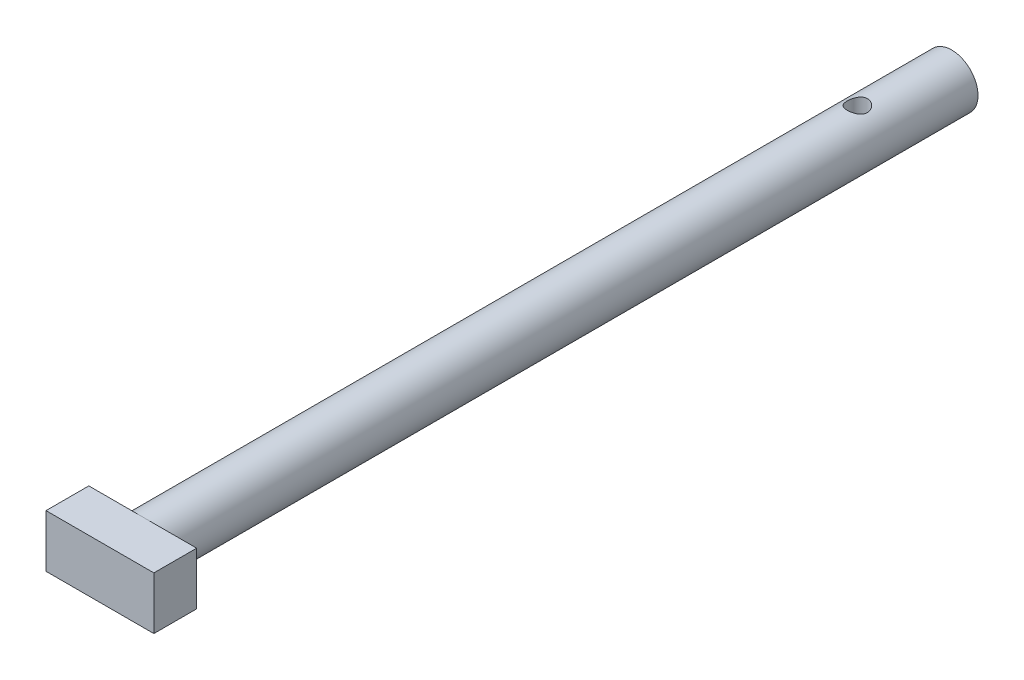
SolidWorks part; units mm, degrees
ref_plane "Front Plane" through (0, 0, 0) normal (0, 0, 1) x (1, 0, 0)
ref_plane "Top Plane" through (0, 0, 0) normal (0, 1, 0) x (1, 0, 0)
ref_plane "Right Plane" through (0, 0, 0) normal (1, 0, 0) x (0, 0, -1)
sketch "Sketch1" plane through (0, 0, 0) normal (0, 0, 1) x (1, 0, 0)
  circle A0 centre (0, 0) radius 1.95
  dimension "D1" = 3.9
extrude "Boss-Extrude1" add sketch "Sketch1" along normal blind 60
sketch "Sketch2" plane through (0, 0, 60) normal (0, 0, 1) x (1, 0, 0)
  line L1 (-4, 1.95) -> (4, 1.95)
  line L2 (-4, 1.95) -> (-4, -1.95)
  line L3 (-4, -1.95) -> (4, -1.95)
  line L4 (4, 1.95) -> (4, -1.95)
  point P4 (0, 1.95)
  point P5 (-4, 0)
  dimension "D1" = 3.9
  dimension "D2" = 8
extrude "Boss-Extrude2" add sketch "Sketch2" along normal blind 3.175
sketch "Sketch3" plane through (0, 1.95, 0) normal (0, 1, 0) x (1, 0, 0)
  circle A0 centre (0, -7) radius 0.75
  point P2 (0, 0)
  dimension "D1" = 7
  dimension "D2" = 1.5
extrude "Cut-Extrude1" cut sketch "Sketch3" against normal blind 5
